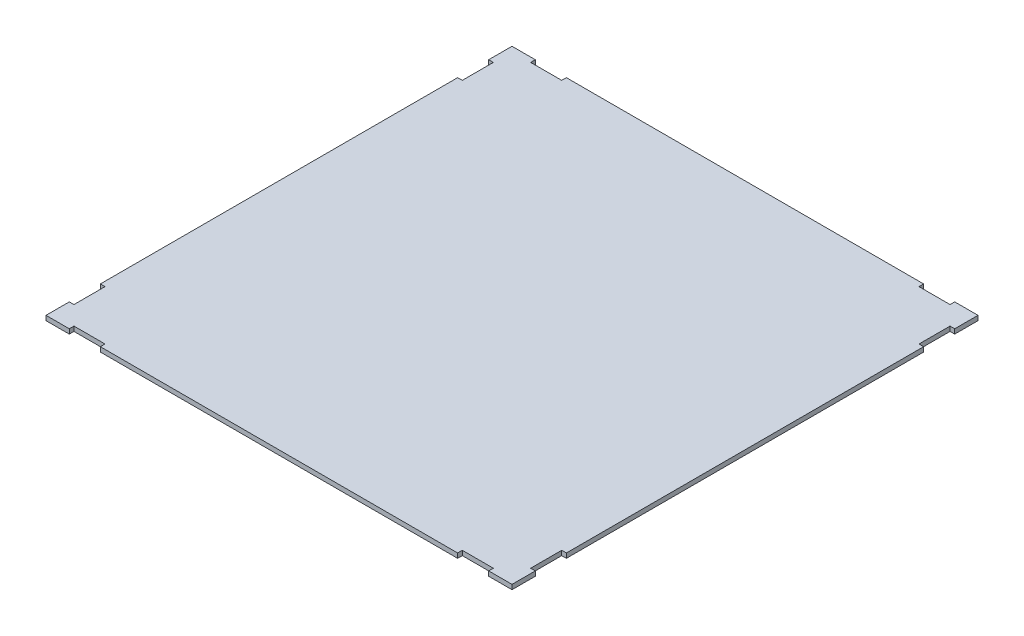
SolidWorks part; units mm, degrees
ref_plane "Alzado" through (0, 0, 0) normal (0, 0, 1) x (1, 0, 0)
ref_plane "Planta" through (0, 0, 0) normal (0, 1, 0) x (1, 0, 0)
ref_plane "Vista lateral" through (0, 0, 0) normal (1, 0, 0) x (0, 0, -1)
sketch "Croquis1" plane through (0, 0, 0) normal (0, 1, 0) x (1, 0, 0)
  line L0 (0, 0) -> (15, 0)
  line L1 (300, 0) -> (300, 15)
  line L2 (300, 300) -> (285, 300)
  line L3 (0, 300) -> (0, 285)
  line L5 (15, 0) -> (15, 3)
  line L6 (15, 3) -> (35, 3)
  line L7 (35, 3) -> (35, 0)
  line L8 (35, 0) -> (265, 0)
  line L9 (0, 0) -> (0, 15)
  line L10 (0, 15) -> (3, 15)
  line L11 (3, 15) -> (3, 35)
  line L12 (3, 35) -> (0, 35)
  line L14 (300, 0) -> (285, 0)
  line L15 (285, 0) -> (285, 3)
  line L16 (285, 3) -> (265, 3)
  line L17 (265, 3) -> (265, 0)
  line L20 (300, 15) -> (297, 15)
  line L21 (297, 15) -> (297, 35)
  line L22 (297, 35) -> (300, 35)
  line L23 (300, 300) -> (300, 285)
  line L24 (300, 35) -> (300, 265)
  line L25 (300, 285) -> (297, 285)
  line L26 (297, 285) -> (297, 265)
  line L27 (297, 265) -> (300, 265)
  line L30 (285, 300) -> (285, 297)
  line L31 (285, 297) -> (265, 297)
  line L32 (265, 297) -> (265, 300)
  line L33 (265, 300) -> (35, 300)
  line L34 (0, 300) -> (15, 300)
  line L35 (15, 300) -> (15, 297)
  line L36 (15, 297) -> (35, 297)
  line L37 (35, 297) -> (35, 300)
  line L40 (0, 285) -> (3, 285)
  line L41 (3, 285) -> (3, 265)
  line L42 (3, 265) -> (0, 265)
  line L43 (0, 265) -> (0, 35)
  dimension "D1" = 300
  dimension "D2" = 300
  dimension "D3" = 300
  dimension "D4" = 20
  dimension "D5" = 15
  dimension "D6" = 3
  dimension "D7" = 20
  dimension "D8" = 15
  dimension "D9" = 3
  dimension "D10" = 20
  dimension "D11" = 15
  dimension "D12" = 3
  dimension "D13" = 20
  dimension "D14" = 15
  dimension "D15" = 3
  dimension "D16" = 15
  dimension "D17" = 20
  dimension "D18" = 3
  dimension "D19" = 15
  dimension "D20" = 20
  dimension "D21" = 3
  dimension "D22" = 20
  dimension "D23" = 3
  dimension "D24" = 15
  dimension "D25" = 20
  dimension "D26" = 15
  dimension "D27" = 3
extrude "Saliente-Extruir1" add sketch "Croquis1" along normal blind 3
